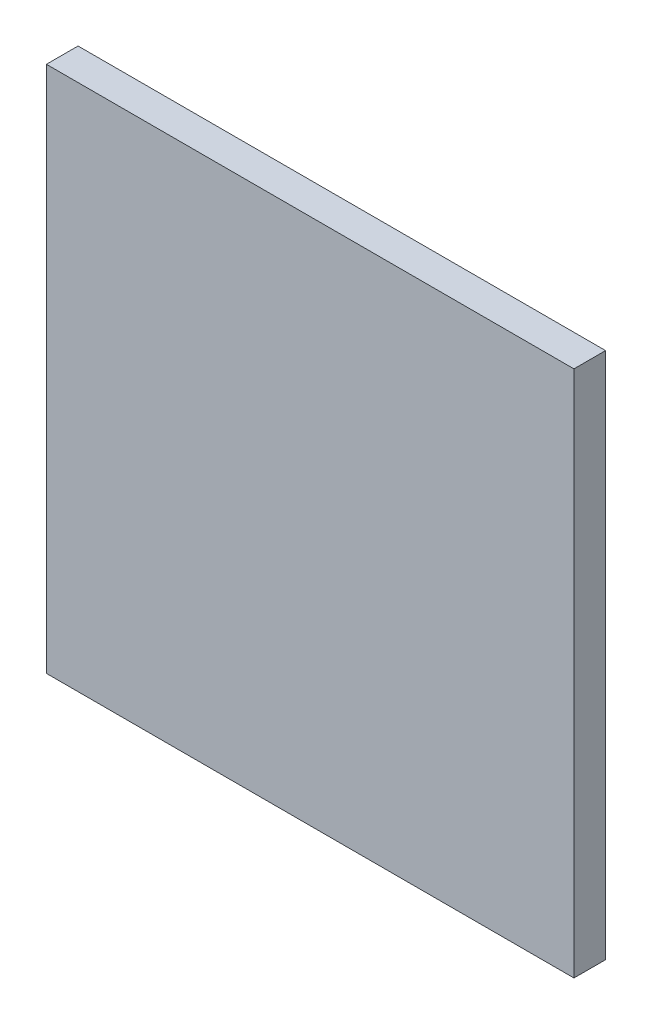
SolidWorks part; units mm, degrees
ref_plane "Front Plane" through (0, 0, 0) normal (0, 0, 1) x (1, 0, 0)
ref_plane "Top Plane" through (0, 0, 0) normal (0, 1, 0) x (1, 0, 0)
ref_plane "Right Plane" through (0, 0, 0) normal (1, 0, 0) x (0, 0, -1)
sketch "Sketch1" plane through (0, 0, 0) normal (0, 0, 1) x (1, 0, 0)
  line L1 (-25, 25) -> (25, 25)
  line L2 (-25, 25) -> (-25, -25)
  line L3 (-25, -25) -> (25, -25)
  line L4 (25, 25) -> (25, -25)
  line L5 (-25, 25) -> (25, -25) construction
  line L6 (-25, -25) -> (25, 25) construction
  point P0 (0, 0)
  dimension "D1" = 50
  dimension "D2" = 50
extrude "Boss-Extrude1" add sketch "Sketch1" along normal blind 3
